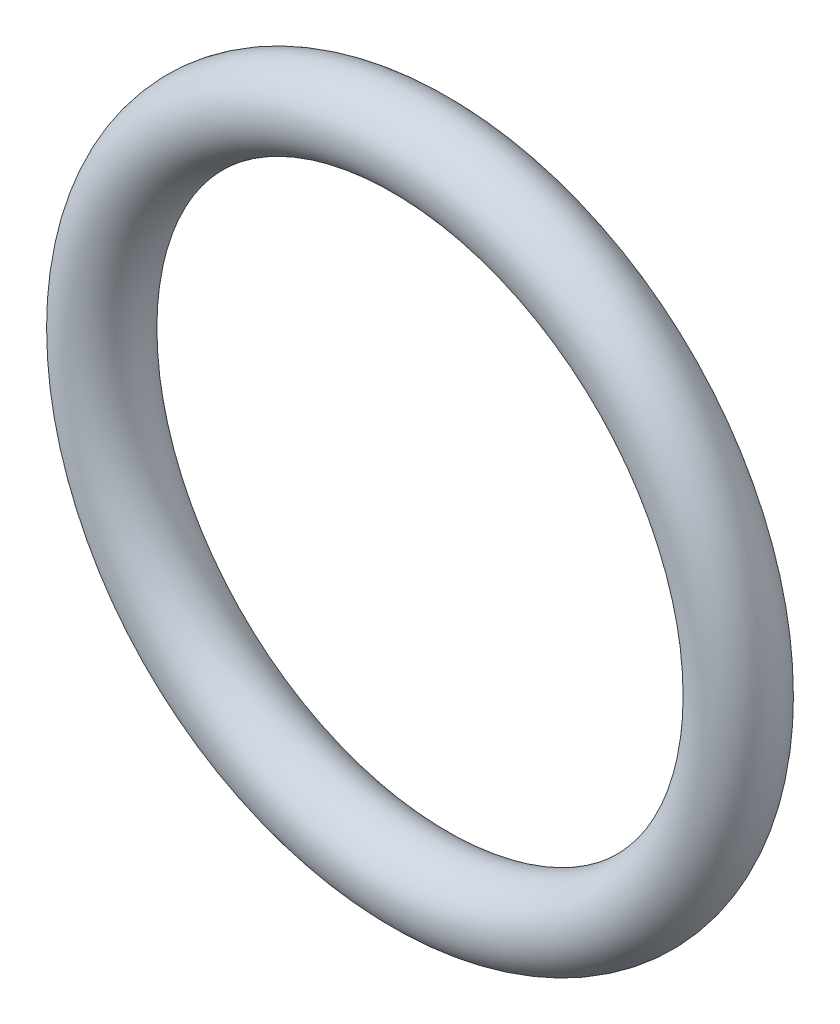
SolidWorks part; units mm, degrees
ref_plane "Front" through (0, 0, 0) normal (0, 0, 1) x (1, 0, 0)
ref_plane "Top" through (0, 0, 0) normal (0, 1, 0) x (1, 0, 0)
ref_plane "Right" through (0, 0, 0) normal (1, 0, 0) x (0, 0, -1)
sketch "Sketch1" plane through (0, 0, 0) normal (1, 0, 0) x (0, -1, 0)
  line L0 (0, -1.3081) -> (0, 1.3081) construction
  line L2 (-13.1737, 0) -> (13.1737, 0) construction
  line L3 (-9.3599, 0) -> (9.3599, 0) construction
  circle A0 centre (10.668, 0) radius 1.3081
  point P9 (9.3599, 0)
  point P10 (11.9761, 0)
  point P13 (10.668, 1.3081)
  point P14 (10.668, -1.3081)
  dimension "Width" = 2.6162
  dimension "ID" = 18.7198
revolve "Revolve1" add sketch "Sketch1" angle 360 about L0
